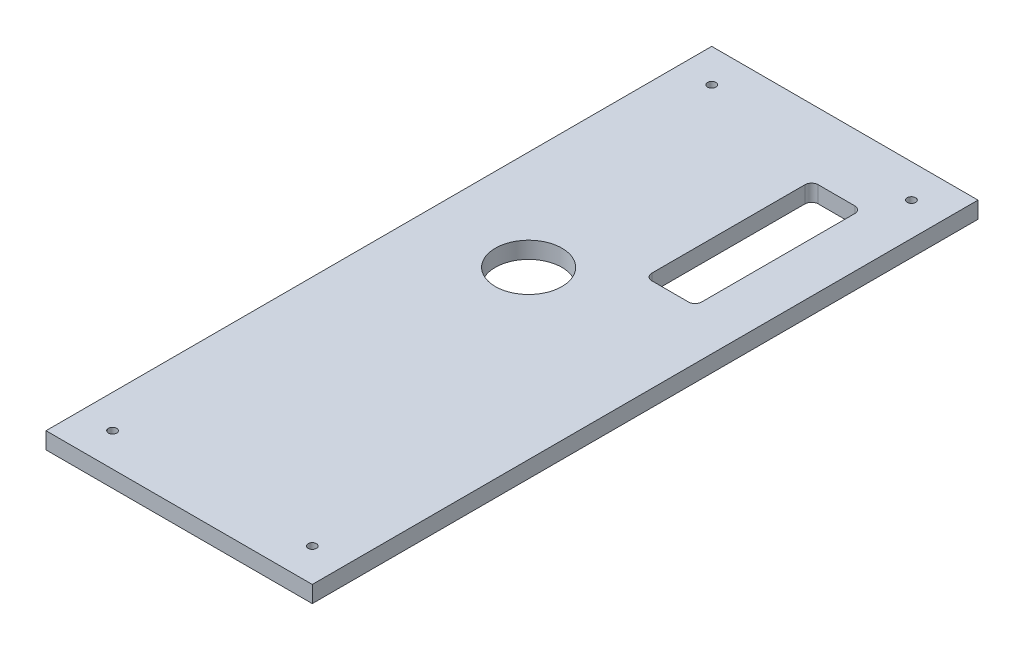
SolidWorks part; units mm, degrees
ref_plane "Front Plane" through (0, 0, 0) normal (0, 0, 1) x (1, 0, 0)
ref_plane "Top Plane" through (0, 0, 0) normal (0, 1, 0) x (1, 0, 0)
ref_plane "Right Plane" through (0, 0, 0) normal (1, 0, 0) x (0, 0, -1)
sketch "Sketch1" plane through (0, 0, 0) normal (0, 1, 0) x (1, 0, 0)
  line L0 (-50.8, 114.3) -> (50.8, 114.3) construction
  line L1 (50.8, -127) -> (-50.8, -127)
  line L2 (50.8, -127) -> (50.8, 127)
  line L3 (50.8, 127) -> (-50.8, 127)
  line L4 (-50.8, -127) -> (-50.8, 127)
  line L5 (50.8, -127) -> (-50.8, 127) construction
  line L6 (50.8, 127) -> (-50.8, -127) construction
  line L7 (29.21, 101.6) -> (15.24, 101.6)
  line L8 (31.75, 99.06) -> (31.75, 40.64)
  line L9 (29.21, 38.1) -> (15.24, 38.1)
  line L10 (12.7, 99.06) -> (12.7, 40.64)
  line L11 (-38.1, 127) -> (-38.1, -127) construction
  line L12 (-50.8, -114.3) -> (50.8, -114.3) construction
  line L13 (38.1, -127) -> (38.1, 127) construction
  circle A0 centre (-12.7, 19.05) radius 12.7
  arc A1 (15.24, 38.1) -> (12.7, 40.64) centre (15.24, 40.64) cw
  arc A2 (31.75, 40.64) -> (29.21, 38.1) centre (29.21, 40.64) cw
  arc A3 (29.21, 101.6) -> (31.75, 99.06) centre (29.21, 99.06) cw
  arc A4 (15.24, 101.6) -> (12.7, 99.06) centre (15.24, 99.06) ccw
  circle A5 centre (-38.1, -114.3) radius 1.5875
  circle A6 centre (38.1, -114.3) radius 1.5875
  circle A7 centre (38.1, 114.3) radius 1.5875
  circle A8 centre (-38.1, 114.3) radius 1.5875
  point P0 (0, 0)
  point P12 (-25.4, 19.05)
  point P13 (-12.7, 31.75)
  point P16 (12.7, 38.1)
  point P19 (31.75, 38.1)
  point P22 (31.75, 101.6)
  point P33 (-38.1, 114.3)
  point P35 (-38.1, -114.3)
  point P36 (38.1, -114.3)
  point P37 (38.1, 114.3)
  dimension "D2" = 25.4
  dimension "D10" = 2.54
  dimension "D11" = 3.175
  dimension "D1" = 101.6
  dimension "D3" = 19.05
  dimension "D4" = 19.05
  dimension "D5" = 63.5
  dimension "D6" = 25.4
  dimension "D7" = 95.25
  dimension "D8" = 25.4
  dimension "D9" = 254
  dimension "D12" = 12.7
  dimension "D13" = 12.7
  dimension "D14" = 12.7
  dimension "D15" = 12.7
extrude "Boss-Extrude1" add sketch "Sketch1" along normal blind 6.35 contours L4 L3 L2 L1
